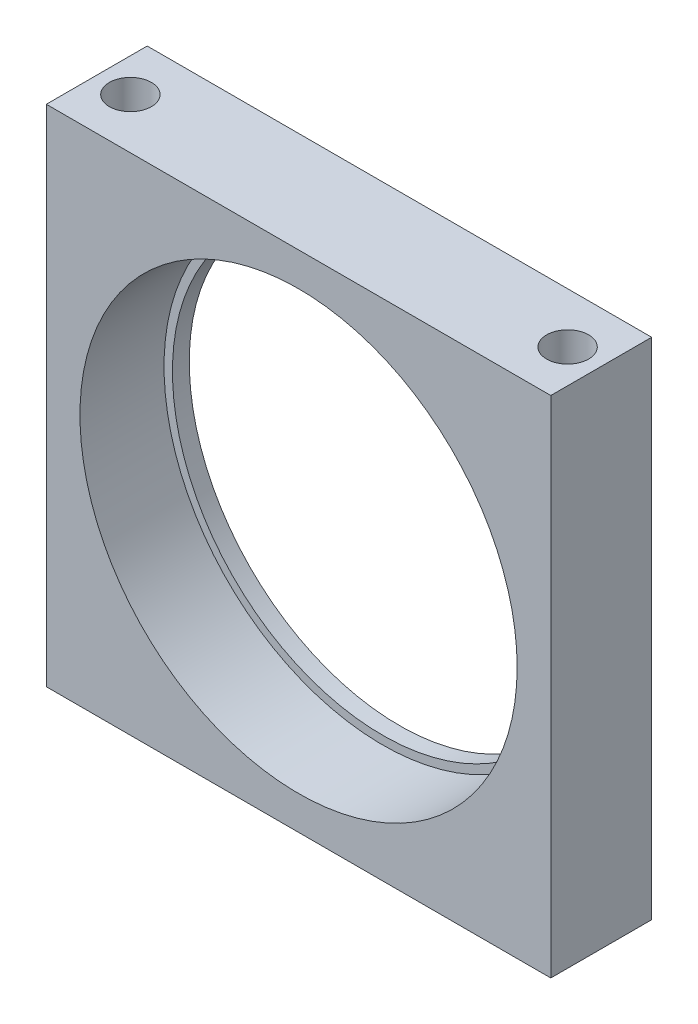
SolidWorks part; units mm, degrees
ref_plane "Plan de face" through (0, 0, 0) normal (0, 0, 1) x (1, 0, 0)
ref_plane "Plan de dessus" through (0, 0, 0) normal (0, 1, 0) x (1, 0, 0)
ref_plane "Plan de droite" through (0, 0, 0) normal (1, 0, 0) x (0, 0, -1)
sketch "Esquisse1" plane through (0, 0, 0) normal (0, 0, 1) x (1, 0, 0)
  line L1 (0, 0) -> (30, 0)
  line L2 (0, 0) -> (0, 30)
  line L3 (0, 30) -> (30, 30)
  line L4 (30, 0) -> (30, 30)
  circle A0 centre (15, 15) radius 12.5
  dimension "D3" = 25
  dimension "D1" = 30
  dimension "D2" = 30
  dimension "D4" = 15
  dimension "D5" = 15
extrude "Boss.-Extru.1" add sketch "Esquisse1" along normal blind 6
sketch "Esquisse3" plane through (0, 0, 6) normal (0, 0, 1) x (1, 0, 0)
  line L0 (0, 30) -> (0, 0) construction
  line L2 (0, 0) -> (30, 0) construction
  circle A0 centre (15, 15) radius 13
  point P6 (14.1794, 0)
  dimension "D3" = 26
  dimension "D1" = 15
  dimension "D2" = 15
extrude "Enlèv. mat.-Extru.1" cut sketch "Esquisse3" against normal blind 5
hole_wizard "Trou pour taraudage pour trou taraudé M31" positions "Esquisse6" profile "Esquisse7" hole size "M3" standard "ISO"
sketch "Esquisse6" plane through (0, 30, 0) normal (0, 1, 0) x (1, 0, 0)
  line L0 (0, -6) -> (0, 0) construction
  line L1 (30, -6) -> (30, 0) construction
  line L2 (30, 0) -> (0, 0) construction
  point P0 (2, -3)
  point P2 (28, -3)
  dimension "D1" = 2
  dimension "D2" = 2
  dimension "D3" = 3
  dimension "D4" = 3
sketch "Esquisse7" plane through (2, 30, 3) normal (1, 0, 0) x (0, 0, 1)
  line L0 (0, 0) -> (0, 6.7511)
  line L1 (0, 6.7511) -> (1.25, 6)
  line L2 (1.25, 6) -> (1.25, 0)
  line L5 (1.25, 0) -> (0, 0)
  line L10 (0, 6.7511) -> (-1.25, 6) construction
  line L11 (0, -6.35) -> (0, 107.95) construction
  dimension "Diamètre du perçage" = 2.5
  dimension "Profondeur du perçage" = 6
  dimension "Angle de pointe" = 118
hole_wizard "Trou pour taraudage pour trou taraudé M32" positions "Esquisse8" profile "Esquisse9" hole size "M3" standard "ISO"
sketch "Esquisse8" plane through (0, 0, 0) normal (0, -1, 0) x (-1, 0, 0)
  line L0 (-30, -6) -> (-30, 0) construction
  line L1 (0, -6) -> (0, 0) construction
  line L4 (0, -6) -> (-30, -6) construction
  point P0 (-2, -3)
  point P2 (-28, -3)
  point P13 (-0.6726, 0)
  dimension "D1" = 2
  dimension "D2" = 2
  dimension "D3" = 3
  dimension "D4" = 3
sketch "Esquisse9" plane through (2, 0, 3) normal (1, 0, 0) x (0, 0, -1)
  line L0 (0, 0) -> (0, 6.7511)
  line L1 (0, 6.7511) -> (1.25, 6)
  line L2 (1.25, 6) -> (1.25, 0)
  line L5 (1.25, 0) -> (0, 0)
  line L10 (0, 6.7511) -> (-1.25, 6) construction
  line L11 (0, -6.35) -> (0, 107.95) construction
  dimension "Diamètre du perçage" = 2.5
  dimension "Profondeur du perçage" = 6
  dimension "Angle de pointe" = 118
equation "\"D4@Esquisse1\"=\"D2@Esquisse1\"/2"
equation "\"D5@Esquisse1\"=\"D2@Esquisse1\"/2"
